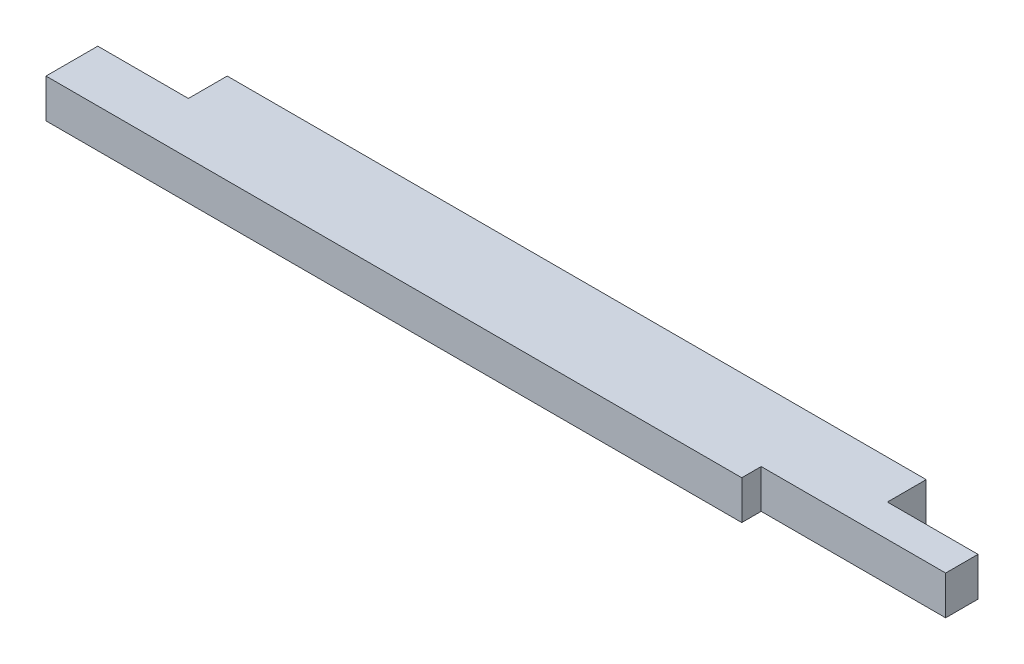
SolidWorks part; units mm, degrees
material "Pine"
ref_plane "Front Plane" through (0, 0, 0) normal (0, 0, 1) x (1, 0, 0)
ref_plane "Top Plane" through (0, 0, 0) normal (0, 1, 0) x (1, 0, 0)
ref_plane "Right Plane" through (0, 0, 0) normal (1, 0, 0) x (0, 0, -1)
sketch "Sketch1" plane through (0, 0, 0) normal (0, 1, 0) x (1, 0, 0)
  line L1 (0, 0) -> (863.6, 0)
  line L2 (0, 0) -> (0, 88.9)
  line L3 (0, 88.9) -> (863.6, 88.9)
  line L4 (863.6, 0) -> (863.6, 88.9)
  dimension "D1" = 88.9
  dimension "D2" = 863.6
extrude "Boss-Extrude1" add sketch "Sketch1" along normal blind 38.1
sketch "Sketch3" plane through (0, 38.1, 0) normal (0, 1, 0) x (1, 0, 0)
  line L1 (0, 88.9) -> (88.9, 88.9)
  line L2 (0, 88.9) -> (0, 50.8)
  line L3 (0, 50.8) -> (88.9, 50.8)
  line L4 (88.9, 88.9) -> (88.9, 50.8)
  line L5 (863.6, 88.9) -> (774.7, 88.9)
  line L6 (863.6, 88.9) -> (863.6, 50.8)
  line L7 (863.6, 50.8) -> (774.7, 50.8)
  line L8 (774.7, 88.9) -> (774.7, 50.8)
  dimension "D1" = 88.9
  dimension "D2" = 88.9
  dimension "D3" = 38.1
  dimension "D4" = 38.1
extrude "Cut-Extrude1" cut sketch "Sketch3" against normal through all
sketch "Sketch4" plane through (0, 38.1, 0) normal (0, 1, 0) x (1, 0, 0)
  line L1 (863.6, 0) -> (682.625, 0)
  line L2 (863.6, 0) -> (863.6, 19.05)
  line L3 (863.6, 19.05) -> (682.625, 19.05)
  line L4 (682.625, 0) -> (682.625, 19.05)
  point P5 (682.625, 9.525)
  dimension "D1" = 180.975
  dimension "D2" = 19.05
extrude "Cut-Extrude2" cut sketch "Sketch4" against normal through all
